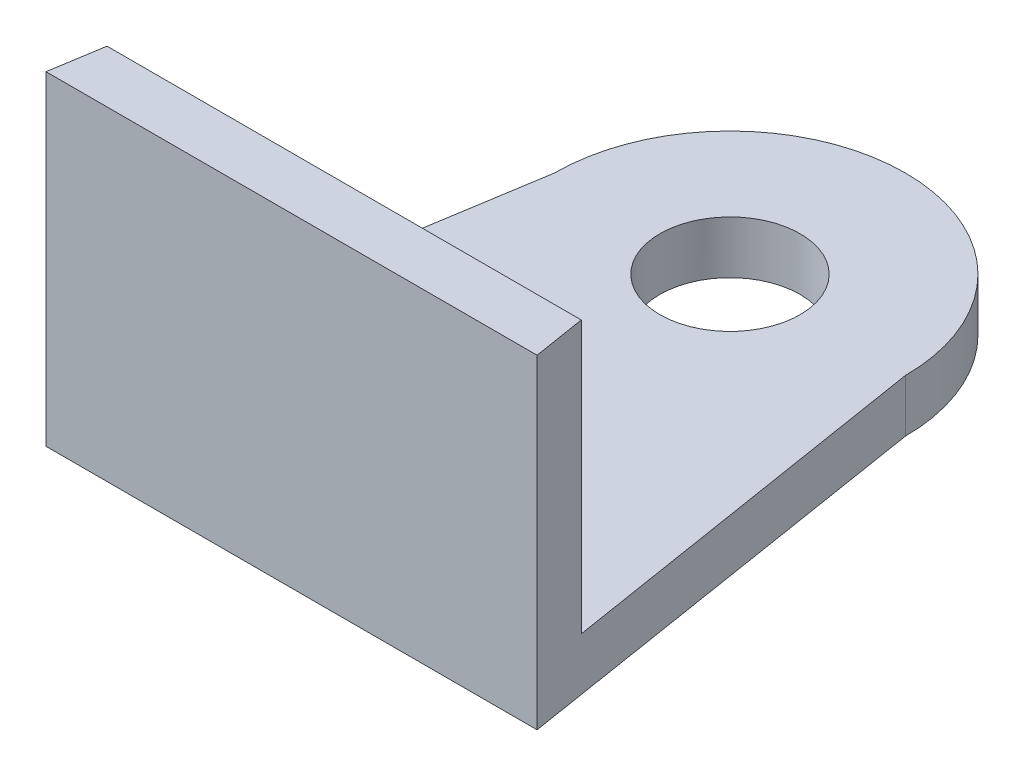
SolidWorks part; units mm, degrees
material "Custom Plastic"
ref_plane "Front Plane" through (0, 0, 0) normal (0, 0, 1) x (1, 0, 0)
ref_plane "Top Plane" through (0, 0, 0) normal (0, 1, 0) x (1, 0, 0)
ref_plane "Right Plane" through (0, 0, 0) normal (1, 0, 0) x (0, 0, -1)
sketch "Sketch1" plane through (0, 0, 0) normal (0, 1, 0) x (1, 0, 0)
  line L0 (-10, 0) -> (-14, -25)
  line L1 (10, 0) -> (14, -25)
  line L2 (0, 17.2103) -> (0, -39.4896) construction
  line L3 (-14, -25) -> (14, -25)
  arc A0 (-10, 0) -> (10, 0) centre (0, 0) cw
  dimension "D1" = 10
  dimension "D2" = 25
  dimension "D3" = 14
extrude "Boss-Extrude1" add sketch "Sketch1" along normal blind 3
sketch "Sketch2" plane through (0, 3, 0) normal (0, 1, 0) x (1, 0, 0)
  line L0 (-21.4034, 0) -> (30.5216, 0) construction
  circle A0 centre (0, 0) radius 4
  dimension "D1" = 8
extrude "Cut-Extrude1" cut sketch "Sketch2" against normal blind 13
sketch "Sketch5" plane through (0, 3, 0) normal (0, 1, 0) x (1, 0, 0)
  line L0 (-13.52, -22) -> (13.52, -22)
  line L1 (-10, 0) -> (-14, -25) construction
  line L2 (14, -25) -> (10, 0) construction
  line L3 (-13.52, -22) -> (-14, -25)
  line L4 (-14, -25) -> (14, -25)
  line L5 (14, -25) -> (13.52, -22)
  dimension "D1" = 3
extrude "Boss-Extrude2" add sketch "Sketch5" along normal blind 15.5
